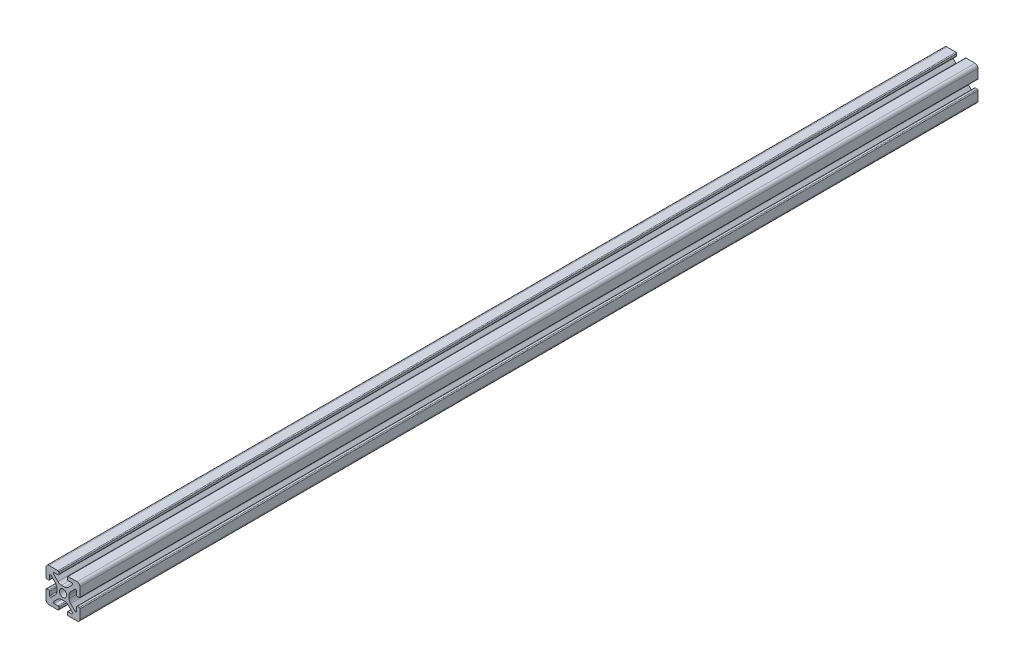
SolidWorks part; units mm, degrees
ref_plane "Front Plane" through (0, 0, 0) normal (0, 0, 1) x (1, 0, 0)
ref_plane "Top Plane" through (0, 0, 0) normal (0, 1, 0) x (1, 0, 0)
ref_plane "Right Plane" through (0, 0, 0) normal (1, 0, 0) x (0, 0, -1)
sketch "Sketch2" plane through (0, 0, 0) normal (0, 0, 1) x (1, 0, 0)
  line L0 (0, 10) -> (0, -10) construction
  line L1 (-10, 0) -> (10, 0) construction
  line L2 (2.5, -10) -> (10, -10)
  line L3 (10, -10) -> (10, -2.5)
  line L4 (2.5, -10) -> (2.5, -7.9246)
  line L5 (2.5, -7.9246) -> (6.4571, -7.9246)
  line L6 (6.4571, -7.9246) -> (2.1325, -3.6)
  line L7 (0, 0) -> (10, -10) construction
  line L8 (10, -2.5) -> (7.9246, -2.5)
  line L9 (7.9246, -2.5) -> (7.9246, -6.4571)
  line L10 (7.9246, -6.4571) -> (3.6, -2.1325)
  line L11 (5.7623, -4.2948) -> (4.2948, -5.7623) construction
  circle A0 centre (0, 0) radius 2.15
  arc A1 (5.25, -7.9246) -> (5.6036, -7.0711) centre (5.25, -7.4246) ccw construction
  point P8 (0, -3.6)
  point P16 (5.0286, -5.0286)
  dimension "Center Hole Diameter" = 4.3
  dimension "D3" = 0.5
  dimension "Rail Height" = 20
  dimension "Rail Width" = 20
  dimension "T-Slot Width" = 5
  dimension "Slot Depth" = 6.4
  dimension "Slot Inner Width" = 11.5
sketch "Sketch3" plane through (0, 0, 0) normal (1, 0, 0) x (0, 0, -1)
  line L0 (-264, -10) -> (264, -10) construction
  line L1 (-238.6, 0) -> (238.6, 0) construction
  dimension "Length" = 528
  dimension "D1" = 25.4
sketch "Sketch4" plane through (0, 0, 0) normal (0, 0, 1) x (1, 0, 0)
  line L0 (3, -10) -> (8.25, -10)
  line L1 (2.5, -10) -> (10, -10) construction
  line L2 (2.5, -10) -> (2.5, -7.9246) construction
  line L3 (2.5, -7.9246) -> (6.4571, -7.9246) construction
  line L4 (2.5, -8.4246) -> (2.5, -9.5)
  line L5 (3, -7.9246) -> (5.25, -7.9246)
  line L6 (0, -3.6) -> (0.8898, -3.6)
  line L7 (6.4571, -7.9246) -> (2.1325, -3.6) construction
  line L8 (3.0112, -4.4787) -> (5.6036, -7.0711)
  line L9 (10, -10) -> (10, -2.5) construction
  line L10 (7.9246, -6.4571) -> (3.6, -2.1325) construction
  line L11 (7.9246, -2.5) -> (7.9246, -6.4571) construction
  line L12 (7.9246, -5.25) -> (7.9246, -3)
  line L13 (10, -2.5) -> (7.9246, -2.5) construction
  line L14 (8.4246, -2.5) -> (9.5, -2.5)
  line L15 (10, -3) -> (10, -8.25)
  line L16 (7.0711, -5.6036) -> (4.4787, -3.0112)
  line L17 (3.6, 0) -> (3.6, -0.8898)
  line L18 (-10, 0) -> (10, 0) construction
  line L19 (0, -3.6) -> (0, -2.15)
  line L20 (0, 10) -> (0, -10) construction
  line L21 (3.6, 0) -> (2.15, 0)
  arc A0 (2.5, -9.5) -> (3, -10) centre (3, -9.5) ccw
  arc A1 (5.25, -7.9246) -> (5.6036, -7.0711) centre (5.25, -7.4246) ccw construction
  arc A2 (2.5, -8.4246) -> (3, -7.9246) centre (3, -8.4246) cw
  arc A3 (5.25, -7.9246) -> (5.6036, -7.0711) centre (5.25, -7.4246) ccw
  arc A4 (0.8898, -3.6) -> (3.0112, -4.4787) centre (0.8898, -6.6) cw
  arc A5 (8.25, -10) -> (10, -8.25) centre (8.25, -8.25) ccw
  arc A6 (7.0711, -5.6036) -> (7.9246, -5.25) centre (7.4246, -5.25) ccw
  arc A7 (7.9246, -3) -> (8.4246, -2.5) centre (8.4246, -3) cw
  arc A8 (9.5, -2.5) -> (10, -3) centre (9.5, -3) cw
  arc A9 (4.4787, -3.0112) -> (3.6, -0.8898) centre (6.6, -0.8898) cw
  circle A10 centre (0, 0) radius 2.15 construction
  arc A11 (0, -2.15) -> (2.15, 0) centre (0, 0) ccw
  dimension "D1" = 1.75
  dimension "D2" = 3
extrude "Boss-Extrude1" add sketch "Sketch4" along normal mid plane 528
mirror "Mirror1" about plane through (0, 0, 0) normal (1, 0, 0) of bodies 134
mirror "Mirror2" about plane through (0, 0, 0) normal (0, 1, 0) of bodies 135
equation "\"D3@Sketch2\"=\"T-Slot Width@Sketch2\"*0.1"
equation "\"D1@Sketch4\"=\"D3@Sketch2\"*3.5"
equation "\"D2@Sketch4\"=\"D3@Sketch2\"*6"
equation "\"D1@Boss-Extrude1\"= \"Length@Sketch3\""
equation "\"Length\" = 528mm"
equation "\"Length@Sketch3\"=\"Length\""
